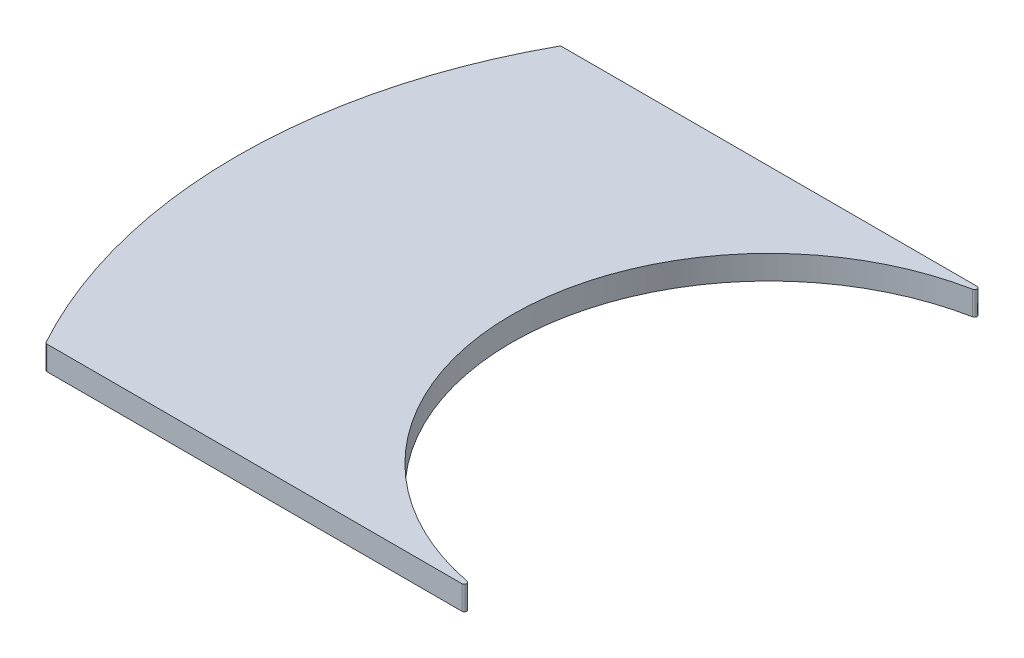
SolidWorks part; units mm, degrees
ref_plane "Front Plane" through (0, 0, 0) normal (0, 0, 1) x (1, 0, 0)
ref_plane "Top Plane" through (0, 0, 0) normal (0, 1, 0) x (1, 0, 0)
ref_plane "Right Plane" through (0, 0, 0) normal (1, 0, 0) x (0, 0, -1)
sketch "Sketch1" plane through (0, 0, 0) normal (0, 1, 0) x (1, 0, 0)
  line L0 (0, 0) -> (0, 22.245) construction
  line L1 (0, 10.76) -> (19.4695, 10.76)
  line L2 (0, 10.76) -> (-19.4695, 10.76)
  line L3 (0, 0) -> (0, -22.245) construction
  line L4 (0, -10.76) -> (19.4695, -10.76)
  line L5 (0, -10.76) -> (-19.4695, -10.76)
  circle A0 centre (0, 0) radius 10.76
  circle A1 centre (0, 0) radius 22.245
  dimension "D1" = 21.52
  dimension "D2" = 44.49
extrude "Boss-Extrude1" add sketch "Sketch1" along normal blind 1 contours L2 A1 L5 A0
fillet "Fillet1" radius 0.1 1 edges at (0, 0.5, 10.76)
fillet "Fillet2" radius 0.1 1 edges at (0, 0.5, -10.76)
fillet "Fillet3" radius 0.1 1 edges at (-19.4695, 0.5, 10.76)
fillet "Fillet4" radius 0.1 1 edges at (-19.4695, 0.5, -10.76)
